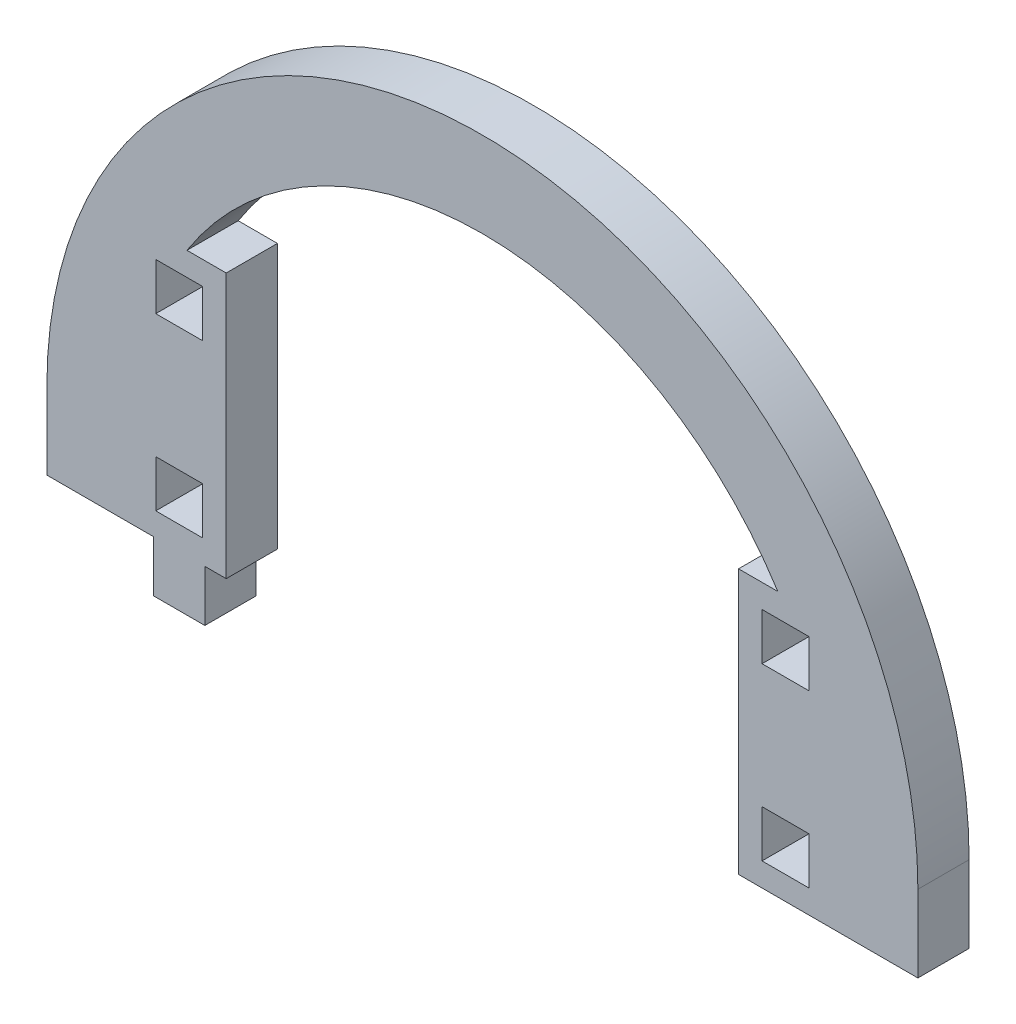
SolidWorks part; units mm, degrees
ref_plane "Front Plane" through (0, 0, 0) normal (0, 0, 1) x (1, 0, 0)
ref_plane "Top Plane" through (0, 0, 0) normal (0, 1, 0) x (1, 0, 0)
ref_plane "Right Plane" through (0, 0, 0) normal (1, 0, 0) x (0, 0, -1)
sketch "Model" plane through (0, 0, 0) normal (0, 0, 1) x (1, 0, 0)
  line L0 (3055.2252, 1478.7447) -> (3055.2252, 1469.7447)
  line L1 (3157.2252, 1478.7447) -> (3157.2252, 1469.7447)
  line L2 (3157.2252, 1469.7447) -> (3147.2252, 1469.7447)
  line L3 (3144.4752, 1477.9947) -> (3138.9752, 1477.9947)
  line L4 (3138.9752, 1477.9947) -> (3138.9752, 1472.4947)
  line L5 (3138.9752, 1472.4947) -> (3144.4752, 1472.4947)
  line L6 (3144.4752, 1472.4947) -> (3144.4752, 1477.9947)
  line L7 (3136.2252, 1469.7447) -> (3147.2252, 1469.7447)
  line L8 (3144.4752, 1497.9947) -> (3138.9752, 1497.9947)
  line L9 (3138.9752, 1497.9947) -> (3138.9752, 1492.4947)
  line L10 (3138.9752, 1492.4947) -> (3144.4752, 1492.4947)
  line L11 (3144.4752, 1492.4947) -> (3144.4752, 1497.9947)
  line L12 (3140.8228, 1500.7447) -> (3136.2252, 1500.7447)
  line L13 (3073.4752, 1477.9947) -> (3067.9752, 1477.9947)
  line L14 (3067.9752, 1477.9947) -> (3067.9752, 1472.4947)
  line L15 (3067.9752, 1472.4947) -> (3073.4752, 1472.4947)
  line L16 (3073.4752, 1472.4947) -> (3073.4752, 1477.9947)
  line L17 (3073.7252, 1469.7447) -> (3076.2252, 1469.7447)
  line L18 (3067.7252, 1469.7447) -> (3067.7252, 1463.7447)
  line L19 (3067.7252, 1463.7447) -> (3073.7252, 1463.7447)
  line L20 (3073.7252, 1463.7447) -> (3073.7252, 1469.7447)
  line L21 (3073.4752, 1497.9947) -> (3067.9752, 1497.9947)
  line L22 (3067.9752, 1497.9947) -> (3067.9752, 1492.4947)
  line L23 (3067.9752, 1492.4947) -> (3073.4752, 1492.4947)
  line L24 (3073.4752, 1492.4947) -> (3073.4752, 1497.9947)
  line L25 (3076.2252, 1500.7447) -> (3071.6275, 1500.7447)
  line L26 (3076.2252, 1500.7447) -> (3076.2252, 1469.7447)
  line L27 (3136.2252, 1500.7447) -> (3136.2252, 1469.7447)
  line L28 (3055.2252, 1469.7447) -> (3067.7252, 1469.7447)
  arc A0 (3157.2252, 1478.7447) -> (3055.2252, 1478.7447) centre (3106.2252, 1478.7447) ccw
  arc A1 (3140.8228, 1500.7447) -> (3071.6275, 1500.7447) centre (3106.2252, 1478.7447) ccw
extrude "Boss-Extrude1" add sketch "Model" along normal blind 6 contours L15 L16 L13 L14 | L23 L24 L21 L22 | L10 L11 L8 L9 | L5 L6 L3 L4 | L0 L28 L18 L19 L20 L17 L26 L25 A1 L12 L27 L7 L2 L1 A0
